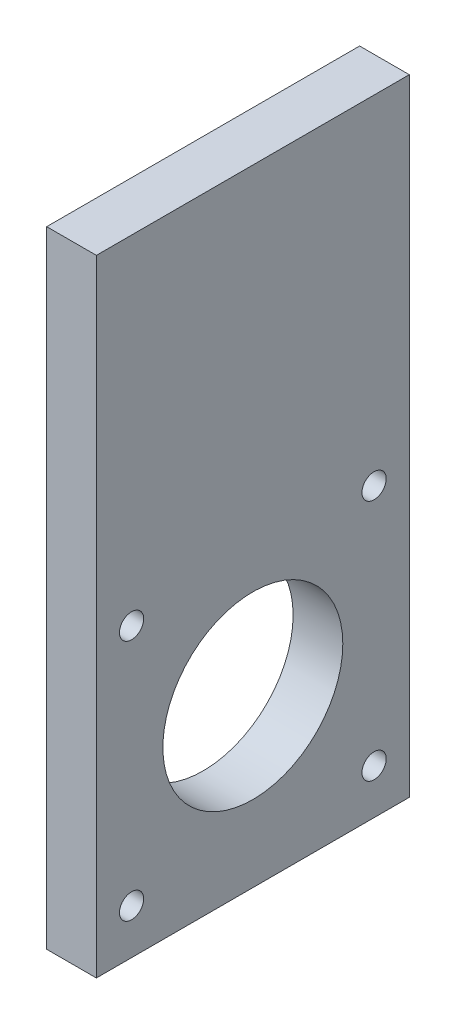
SolidWorks part; units mm, degrees
ref_plane "Front Plane" through (0, 0, 0) normal (0, 0, 1) x (1, 0, 0)
ref_plane "Top Plane" through (0, 0, 0) normal (0, 1, 0) x (1, 0, 0)
ref_plane "Right Plane" through (0, 0, 0) normal (1, 0, 0) x (0, 0, -1)
sketch "Sketch1" plane through (0, 0, 0) normal (1, 0, 0) x (0, 0, -1)
  line L1 (0, 0) -> (-20, 0)
  line L2 (0, 0) -> (0, 80)
  line L3 (0, 80) -> (-20, 80)
  line L4 (-20, 0) -> (-20, 80)
  dimension "D1" = 20
  dimension "D2" = 80
extrude "Boss-Extrude1" add sketch "Sketch1" along normal blind 6.35
sketch "Sketch2" plane through (6.35, 0, 0) normal (1, 0, 0) x (0, 0, -1)
  line L0 (0, 0) -> (0, 80) construction
  line L3 (-20, 0) -> (0, 0) construction
  line L4 (-15.5, 36.75) -> (-20, 36.75) construction
  line L5 (-20, 80) -> (-20, 0) construction
  line L6 (-20, 5.75) -> (-15.5, 5.75) construction
  circle A0 centre (-15.5, 5.75) radius 1.55
  circle A1 centre (-15.5, 36.75) radius 1.55
  dimension "D1" = 3.1
  dimension "D4" = 31
  dimension "D2" = 15.5
  dimension "D3" = 5.75
extrude "Motor Mount Holes" cut sketch "Sketch2" against normal blind 10
sketch "Sketch3" plane through (6.35, 0, 0) normal (1, 0, 0) x (0, 0, -1)
  line L1 (0, 0) -> (0, 80) construction
  line L2 (-15.5, 36.75) -> (-15.5, 5.75) construction
  circle A0 centre (0, 21.25) radius 11.5
  point P2 (-15.5, 21.25)
  dimension "D1" = 23
extrude "Flange Hole" cut sketch "Sketch3" against normal blind 10
mirror "Mirror1" about plane through (6.35, 0, 0) normal (0, 0, 1) of "Boss-Extrude1", "Motor Mount Holes", "Flange Hole"
